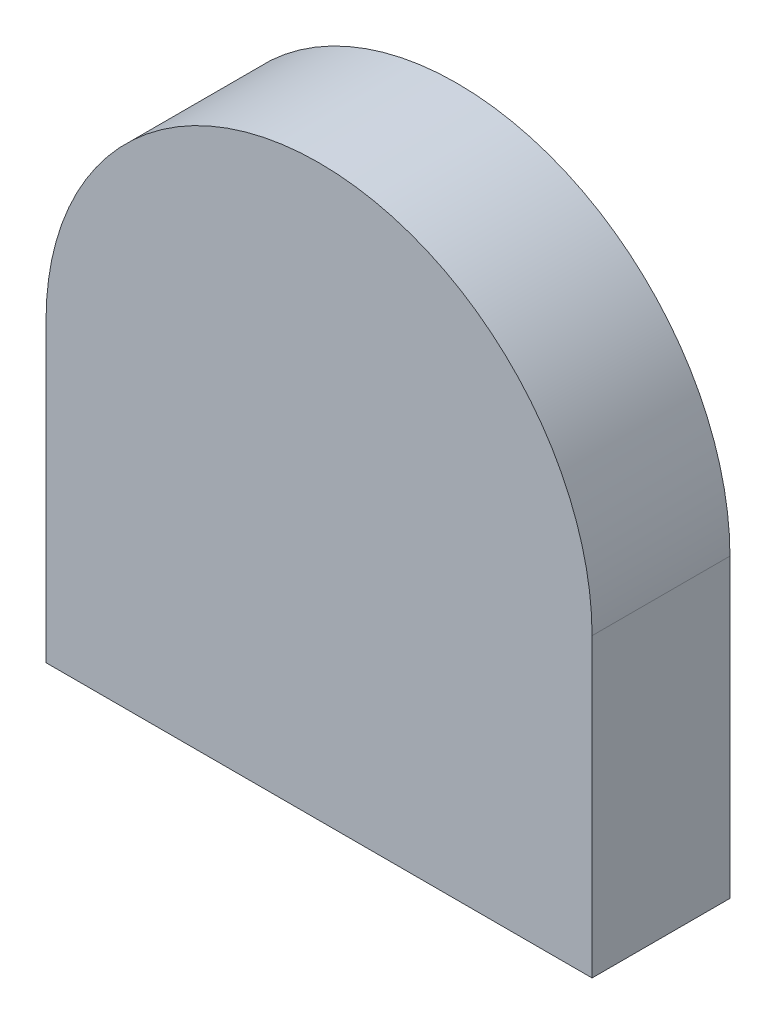
SolidWorks part; units mm, degrees
ref_plane "Płaszczyzna przednia" through (0, 0, 0) normal (0, 0, 1) x (1, 0, 0)
ref_plane "Płaszczyzna górna" through (0, 0, 0) normal (0, 1, 0) x (1, 0, 0)
ref_plane "Płaszczyzna prawa" through (0, 0, 0) normal (1, 0, 0) x (0, 0, -1)
sketch "Szkic1" plane through (0, 0, 0) normal (0, 0, 1) x (1, 0, 0)
  line L0 (0, 0) -> (39.6, 0)
  line L1 (39.6, 0) -> (39.6, 21.5)
  line L2 (0, 0) -> (0, 21.5)
  line L3 (0, 21.5) -> (39.6, 21.5) construction
  arc A0 (0, 21.5) -> (39.6, 21.5) centre (19.8, 21.5) cw
  dimension "D1" = 39.6
  dimension "D2" = 21.5
extrude "Dodanie-wyciągnięcie1" add sketch "Szkic1" along normal blind 10
